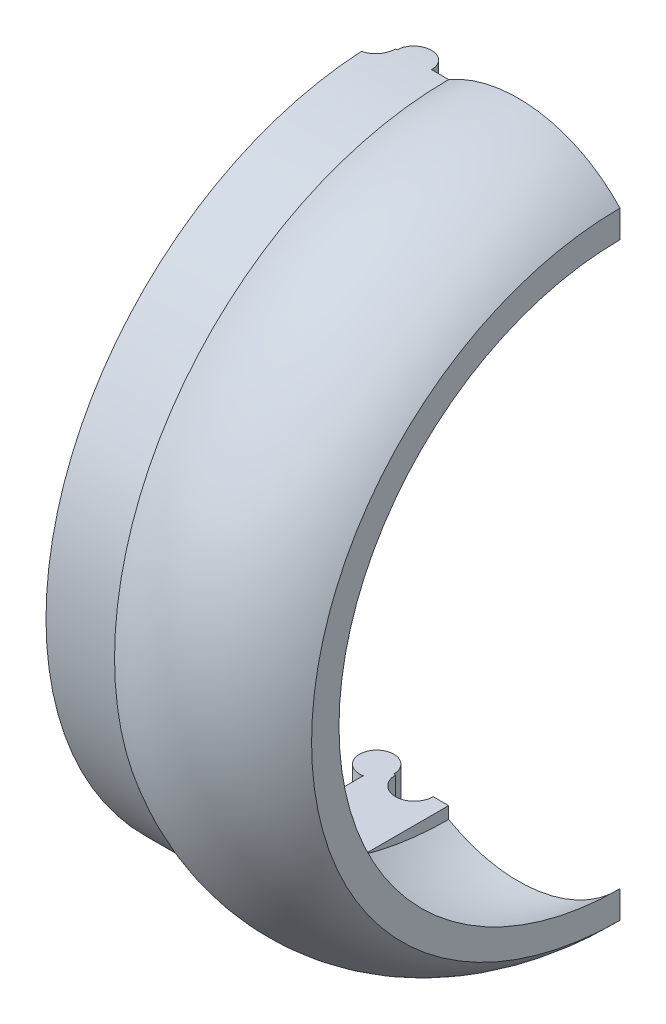
SolidWorks part; units mm, degrees
ref_plane "Front Plane" through (0, 0, 0) normal (0, 0, 1) x (1, 0, 0)
ref_plane "Top Plane" through (0, 0, 0) normal (0, 1, 0) x (1, 0, 0)
ref_plane "Right Plane" through (0, 0, 0) normal (1, 0, 0) x (0, 0, -1)
sketch "Sketch1" plane through (0, 0, 0) normal (0, 0, 1) x (1, 0, 0)
  line L0 (0, 0) -> (0, 89.5) construction
  line L1 (0, 89.5) -> (20, 89.5)
  line L2 (0, 89.5) -> (0, 97.5)
  line L3 (0, 97.5) -> (20, 97.5)
  line L4 (70, 90) -> (70, 82)
  line L5 (70, 82) -> (0, 0) construction
  line L6 (0, 0) -> (70, 0) construction
  line L7 (70, 0) -> (70, 82) construction
  arc A1 (20, 89.5) -> (70, 82) centre (40.2991, 54.4107) cw
  arc A2 (20, 97.5) -> (70, 90) centre (40.2991, 62.4107) cw
  point P11 (46.3125, 94.5)
  dimension "D1" = 89.5
  dimension "D2" = 20
  dimension "D3" = 8
  dimension "D4" = 82
  dimension "D5" = 5
  dimension "D6" = 50
revolve "Revolve1" add sketch "Sketch1" angle 180 about L6
sketch "Sketch3" plane through (0, 0, 0) normal (-1, 0, 0) x (0, 0, 1)
  line L0 (0, 89.5) -> (0, -89.5) construction
  line L1 (0, 89.5) -> (0, 86)
  line L2 (0, 86) -> (24.7841, 86)
  line L3 (0, -89.5) -> (0, -86)
  line L4 (0, -86) -> (24.7841, -86)
  arc A0 (0, -89.5) -> (0, 89.5) centre (0, 0) ccw construction
  arc A1 (0, -89.5) -> (24.7841, -86) centre (0, 0) ccw
  arc A2 (24.7841, 86) -> (0, 89.5) centre (0, 0) ccw
  arc A3 (24.7841, -86) -> (24.7841, 86) centre (0, 0) ccw construction
  arc M5 (0, 89.5) -> (0, -89.5) centre (0, 0) cw
  dimension "D1" = 172
extrude "Boss-Extrude1" add sketch "Sketch3" against normal blind 20 contours L1 L2 M5 | L4 L3 M5
sketch "Sketch5" plane through (0, 86, 0) normal (0, -1, 0) x (1, 0, 0)
  line L1 (20, 0) -> (0, 0) construction
  circle A1 centre (10, 0) radius 5
  dimension "D1" = 10
extrude "Boss-Extrude2" add sketch "Sketch5" against normal up to surface (11.3717 mm away)
sketch "Sketch6" plane through (0, -86, 0) normal (0, 1, 0) x (1, 0, 0)
  line L0 (20, 0) -> (0, 0) construction
  circle A0 centre (10, 0) radius 5.5
  dimension "D1" = 11
extrude "Cut-Extrude1" cut sketch "Sketch6" against normal up to surface (11.3447 mm away)
ref_plane "Plane1" through (0, -86, 24.7841) normal (0, 0, 1) x (1, 0, 0)
sketch "Sketch8" plane through (0, -86, 0) normal (0, 1, 0) x (1, 0, 0)
  line L0 (0, 0) -> (-1, 0) construction
  circle A0 centre (-1, 0) radius 5
  dimension "D1" = 10
  dimension "D2" = 1
extrude "Boss-Extrude3" add sketch "Sketch8" against normal up to surface (11.3717 mm away)
sketch "Sketch10" plane through (0, 86, 0) normal (0, -1, 0) x (1, 0, 0)
  line L0 (0, 0) -> (-1, 0) construction
  circle A0 centre (-1, 0) radius 5.5
  dimension "D1" = 11
  dimension "D2" = 1
extrude "Cut-Extrude2" cut sketch "Sketch10" against normal up to surface (11.3447 mm away)
